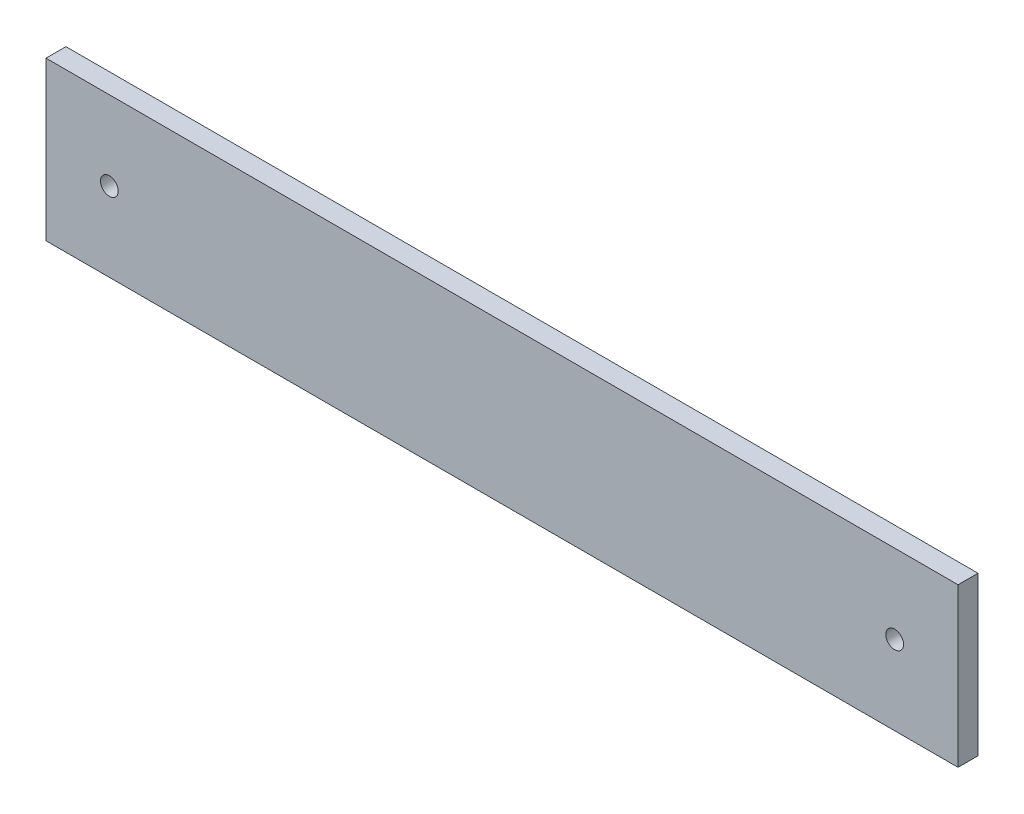
SolidWorks part; units mm, degrees
material "Maple"
ref_plane "Front Plane" through (0, 0, 0) normal (0, 0, 1) x (1, 0, 0)
ref_plane "Top Plane" through (0, 0, 0) normal (0, 1, 0) x (1, 0, 0)
ref_plane "Right Plane" through (0, 0, 0) normal (1, 0, 0) x (0, 0, -1)
sketch "Sketch1" plane through (0, 0, 0) normal (0, 0, 1) x (1, 0, 0)
  line L18 (-83.0174, 25.085) -> (62.1526, 25.085)
  line L19 (-83.0174, 25.085) -> (-83.0174, -0.0872)
  line L20 (-83.0174, -0.0872) -> (62.1526, -0.0872)
  line L23 (62.1526, 25.085) -> (62.1526, -0.0872)
  circle A0 centre (-72.9353, 12.5) radius 1.415
  circle A1 centre (52.0647, 12.5) radius 1.415
  dimension "D3" = 2.83
  dimension "D4" = 2.83
  dimension "D1" = 125
  dimension "D2" = 25.1723
  dimension "D5" = 145.17
extrude "Boss-Extrude1" add sketch "Sketch1" along normal blind 3.175
equation "\"length\"=145"
equation "\"width\"=25"
